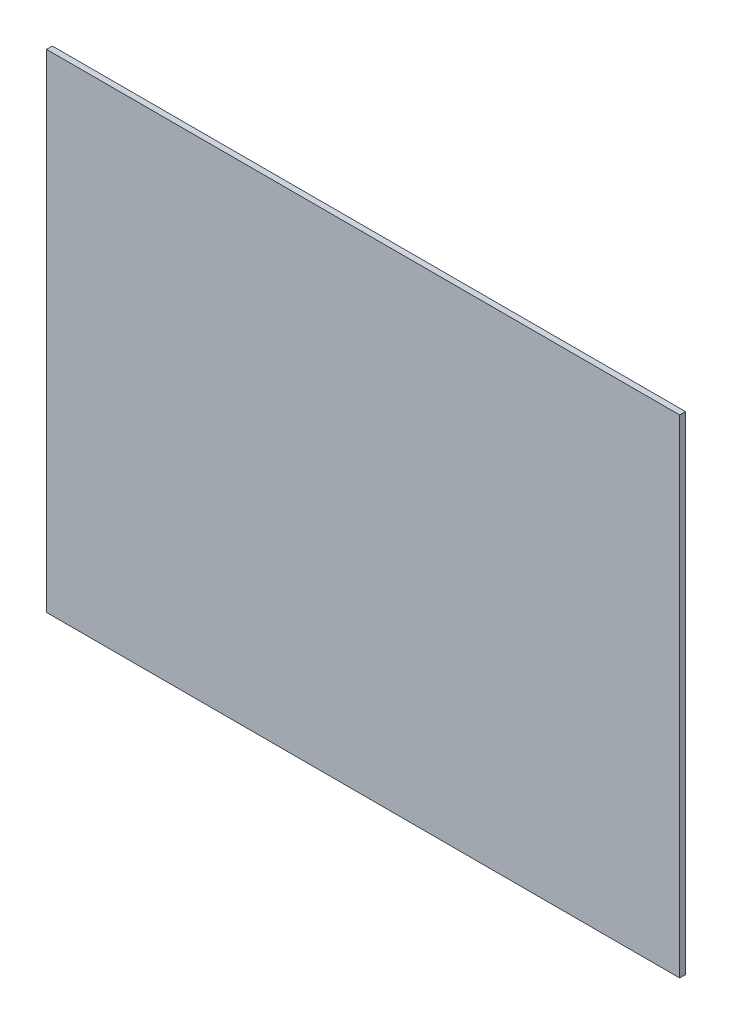
SolidWorks part; units mm, degrees
material "Cam"
ref_plane "Ön Düzlem" through (0, 0, 0) normal (0, 0, 1) x (1, 0, 0)
ref_plane "Üst Düzlem" through (0, 0, 0) normal (0, 1, 0) x (1, 0, 0)
ref_plane "Sağ Düzlem" through (0, 0, 0) normal (1, 0, 0) x (0, 0, -1)
sketch "Çizim1" plane through (0, 0, 0) normal (0, 0, 1) x (1, 0, 0)
  line L1 (-163.1, -125.6) -> (163.1, -125.6)
  line L2 (-163.1, -125.6) -> (-163.1, 125.6)
  line L3 (-163.1, 125.6) -> (163.1, 125.6)
  line L4 (163.1, -125.6) -> (163.1, 125.6)
  line L5 (-163.1, -125.6) -> (163.1, 125.6) construction
  line L6 (-163.1, 125.6) -> (163.1, -125.6) construction
  point P0 (0, 0)
  dimension "D1" = 326.2
  dimension "D2" = 251.2
extrude "Yükseklik-Ekstrüzyon1" add sketch "Çizim1" against normal blind 3
